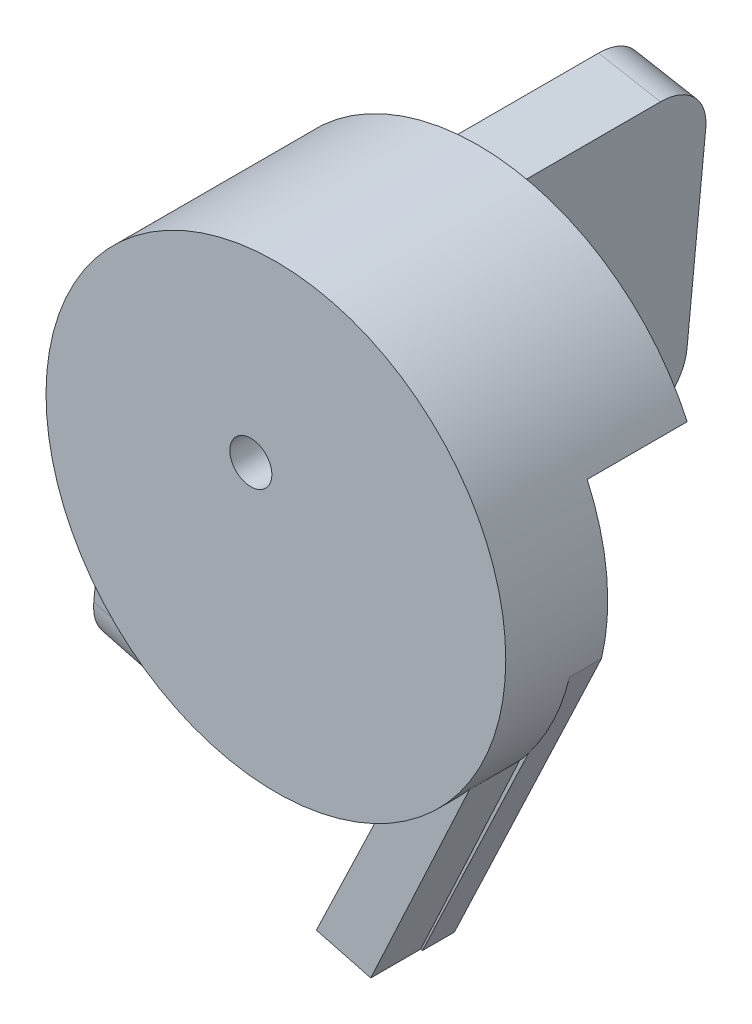
SolidWorks part; units mm, degrees
ref_plane "Front Plane" through (0, 0, 0) normal (0, 0, 1) x (1, 0, 0)
ref_plane "Top Plane" through (0, 0, 0) normal (0, 1, 0) x (1, 0, 0)
ref_plane "Right Plane" through (0, 0, 0) normal (1, 0, 0) x (0, 0, -1)
sketch "Sketch1" plane through (0, 0, 0) normal (0, 0, 1) x (1, 0, 0)
  line L0 (-16.7339, 0.7347) -> (-19.5437, -29.2653)
  line L1 (-19.5437, -29.2653) -> (1.9856, -34.8971)
  line L2 (1.9856, -34.8971) -> (14.8304, -7.786)
  line L3 (0.192, -0.8506) -> (14.8304, -7.786)
  line L4 (-16.7339, 0.7347) -> (0.192, -0.8506)
  line L5 (-22.9127, 2.0023) -> (-25.6907, -27.6574)
  line L6 (-25.6907, -27.6574) -> (7.6604, -36.3816)
  line L7 (7.6604, -36.3816) -> (22.3757, -5.3225)
  circle A0 centre (0, 0) radius 16.75
  circle A1 centre (0, 0) radius 23
  dimension "D2" = 33.5
  dimension "D12" = 0
  dimension "D13" = 46
  dimension "D1" = 0
  dimension "D3" = 16.75
  dimension "D4" = 16.75
  dimension "D5" = 0
  dimension "D6" = 30
  dimension "D7" = 90
  dimension "D10" = 90
  dimension "D11" = 30
  dimension "D14" = 23
  dimension "D15" = 23
  dimension "D16" = 180
  dimension "D17" = 180
  dimension "D19" = 160
extrude "Boss-Extrude3" add sketch "Sketch1" along normal blind 13.2 contours A1 L5 L6 L0 | A1 L0 A0 L2 L7 | A1 L2 L6 L7
sketch "Sketch2" plane through (0, 0, 0) normal (0, 0, -1) x (-1, 0, 0)
  line L0 (22.9127, 2.0023) -> (16.7206, 0.8761)
  line L1 (16.7206, 0.8761) -> (19.5437, -29.2653)
  line L2 (19.5437, -29.2653) -> (25.6907, -27.6574)
  line L3 (25.6907, -27.6574) -> (22.9127, 2.0023)
  line L4 (16.7339, 0.7347) -> (19.5437, -29.2653) construction
  line L5 (22.9127, 2.0023) -> (25.6907, -27.6574) construction
  line L7 (25.6907, -27.6574) -> (19.5437, -29.2653) construction
  point P4 (24.3017, -12.8275)
  point P11 (18.1388, -14.2653)
  dimension "D1" = 0
  dimension "D2" = 0
  dimension "D3" = 180
  dimension "D4" = 0
  dimension "D5" = 0
  dimension "D6" = 0
extrude "Boss-Extrude4" add sketch "Sketch2" along normal blind 40
sketch "Sketch3" plane through (0, 0, 13.2) normal (0, 0, 1) x (1, 0, 0)
  circle A0 centre (0, 0) radius 23
  arc A1 (14.8304, -7.786) -> (-16.7339, 0.7347) centre (0, 0) ccw construction
  dimension "D2" = 46
  dimension "D1" = 0
extrude "Boss-Extrude5" add sketch "Sketch3" along normal blind 7
sketch "Sketch4" plane through (0, 0, 20.2) normal (0, 0, 1) x (1, 0, 0)
  circle A0 centre (-2.506, 4.3267) radius 2.1017
  circle A2 centre (0, 0) radius 23 construction
  dimension "D1" = 5
extrude "Cut-Extrude1" cut sketch "Sketch4" against normal blind 10
sketch "Sketch6" plane through (0, 0, 0) normal (0, 0, -1) x (-1, 0, 0)
  line L1 (-26.1892, 9.4902) -> (-0.4743, 9.4902)
  line L2 (-26.1892, 9.4902) -> (-26.1892, -44.4369)
  line L3 (-26.1892, -44.4369) -> (-0.4743, -44.4369)
  line L4 (-0.4743, 9.4902) -> (-0.4743, -44.4369)
extrude "Cut-Extrude2" cut sketch "Sketch6" against normal blind 10
sketch "Sketch7" plane through (0, 0, 13.2) normal (0, 0, 1) x (1, 0, 0)
  line L0 (2.0506, -34.9141) -> (7.4943, -36.3381)
  line L1 (7.4943, -36.3381) -> (17.7899, -14.1801)
  line L2 (17.7899, -14.1801) -> (12.5045, -13.1112)
  line L3 (12.5045, -13.1112) -> (2.0506, -34.9141)
  line L4 (1.9856, -34.8971) -> (7.6604, -36.3816) construction
  arc M1 (18.2907, -13.9445) -> (8.3693, -21.4232) centre (0, 0) cw
  line M3 (1.9856, -34.8971) -> (7.6604, -36.3816)
  dimension "D1" = 180
  dimension "D2" = 0
extrude "Boss-Extrude6" add sketch "Sketch7" along normal blind 5 contours L3 L1 M1 M3
sketch "Sketch11" plane through (-22.8993, 2.1448, 0) normal (-0.9956, 0.0933, 0) x (0, 0, 1)
  text T0 "GIAU-QUANG" font "Century Gothic" height in points 15
extrude "Cut-Extrude5" cut sketch "Sketch11" against normal blind 5
fillet "Fillet5" radius 5 1 edges at (-22.6172, -28.4613, -40)
fillet "Fillet6" radius 5 1 edges at (-19.8167, 1.4392, -40)
fillet "Fillet7" radius 5 1 edges at (-22.6172, -28.4613, 13.2)
sketch "Sketch12" plane through (-16.6566, 1.5601, 0) normal (0.9956, -0.0933, 0) x (0, 0, -1)
  line L0 (-13.2, -0.829) -> (-13.2, -15.7837) construction
  line L3 (35, -0.687) -> (0, -0.687) construction
  circle A0 centre (18.8, -10.687) radius 1.4
  dimension "D1" = 2.8
  dimension "D2" = 32
  dimension "D3" = 10
extrude "Cut-Extrude6" cut sketch "Sketch12" against normal blind 4
sketch "Sketch13" plane through (-16.6566, 1.5601, 0) normal (0.9956, -0.0933, 0) x (0, 0, -1)
  line L0 (35, -0.687) -> (0, -0.687) construction
  circle A0 centre (26.8, -10.687) radius 1.4
  circle A1 centre (18.8, -10.687) radius 1.4 construction
  dimension "D1" = 2.8
  dimension "D2" = 10
  dimension "D3" = 8
extrude "Cut-Extrude7" cut sketch "Sketch13" against normal blind 4
